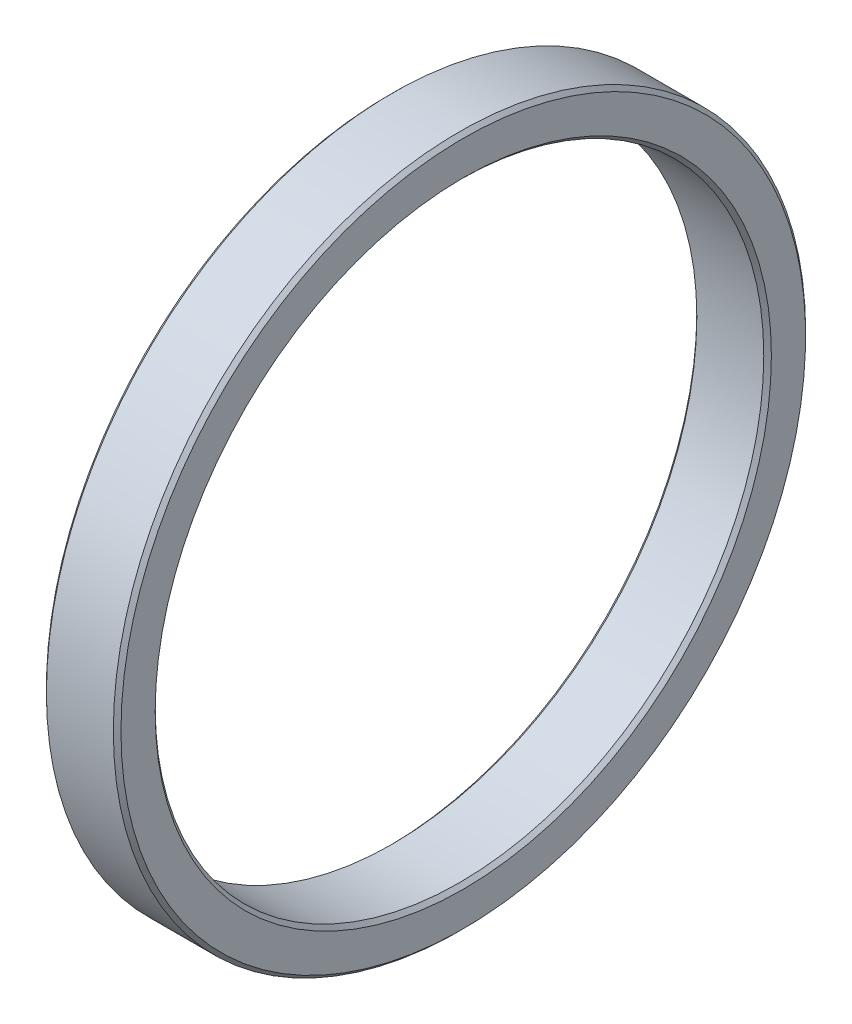
SolidWorks part; units mm, degrees
material "Aluminum Bronze"
ref_plane "Front Plane" through (0, 0, 0) normal (0, 0, 1) x (1, 0, 0)
ref_plane "Top Plane" through (0, 0, 0) normal (0, 1, 0) x (1, 0, 0)
ref_plane "Right Plane" through (0, 0, 0) normal (1, 0, 0) x (0, 0, -1)
sketch "Sketch1" plane through (0, 0, 0) normal (0, 0, 1) x (1, 0, 0)
  line L0 (0, 0) -> (9.8, 0)
  line L1 (9.8, 0) -> (9.8, 45.5)
  line L2 (9.8, 45.5) -> (0, 45.5)
  line L3 (0, 45.5) -> (0, 0)
  line L4 (0, 40) -> (9.8, 40)
  dimension "D1" = 9.8
  dimension "D2" = 45.5
  dimension "D3" = 40
revolve "Revolve1" add sketch "Sketch1" angle 360 about L0
chamfer "Chamfer1" distance 0.5 angle 45 4 edges at (0, 0, 45.5) (9.8, 0, 45.5) (0, 0, 40) (9.8, 0, 40)
